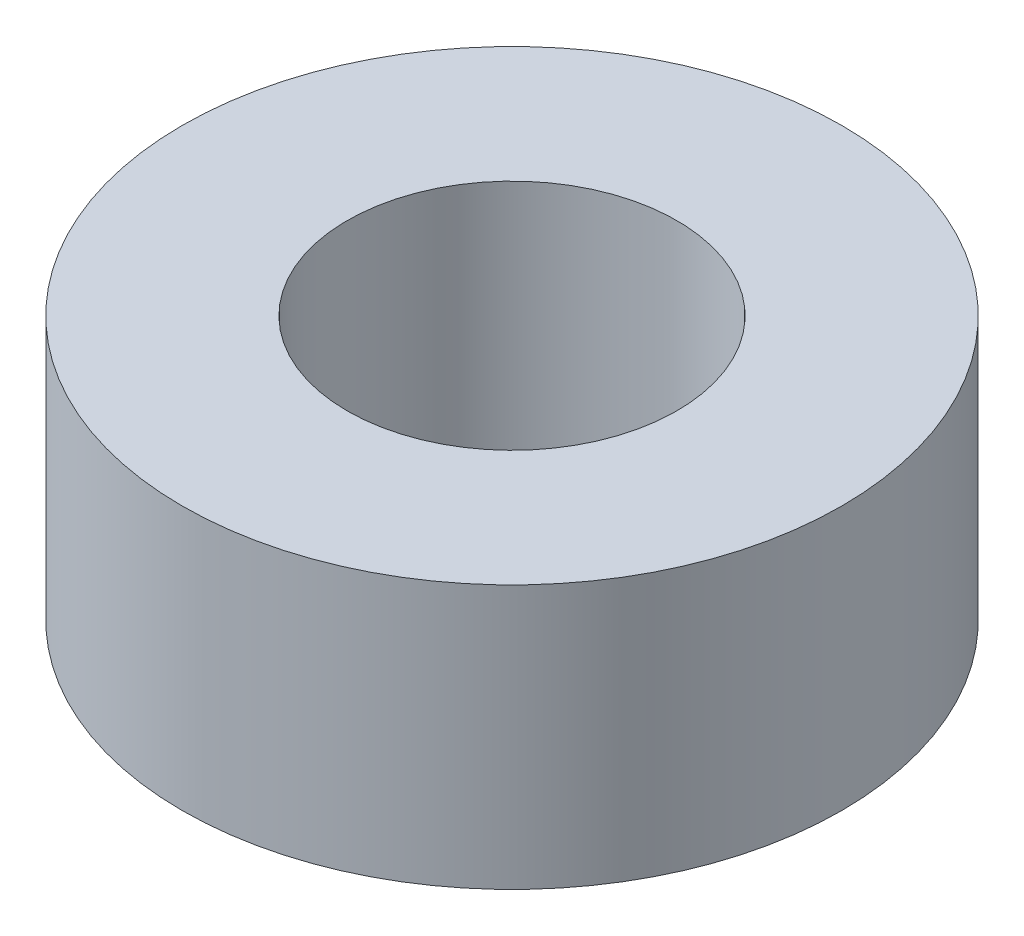
SolidWorks part; units mm, degrees
material "1060 Alloy"
ref_plane "Front Plane" through (0, 0, 0) normal (0, 0, 1) x (1, 0, 0)
ref_plane "Top Plane" through (0, 0, 0) normal (0, 1, 0) x (1, 0, 0)
ref_plane "Right Plane" through (0, 0, 0) normal (1, 0, 0) x (0, 0, -1)
sketch "Sketch1" plane through (0, 0, 0) normal (0, 1, 0) x (1, 0, 0)
  circle A0 centre (0, 0) radius 5
  circle A1 centre (0, 0) radius 2.5
  dimension "D1" = 10
  dimension "D2" = 5
extrude "Boss-Extrude1" add sketch "Sketch1" along normal blind 4
